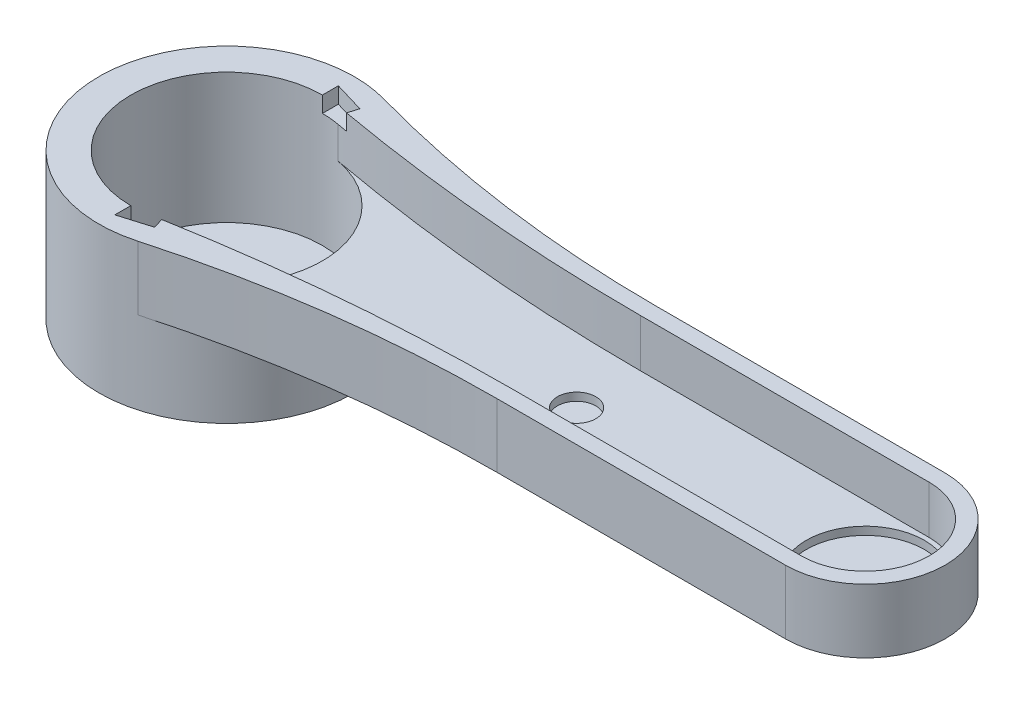
SolidWorks part; units mm, degrees
ref_plane "Front Plane" through (0, 0, 0) normal (0, 0, 1) x (1, 0, 0)
ref_plane "Top Plane" through (0, 0, 0) normal (0, 1, 0) x (1, 0, 0)
ref_plane "Right Plane" through (0, 0, 0) normal (1, 0, 0) x (0, 0, -1)
sketch "Sketch1" plane through (0, 0, 0) normal (0, 1, 0) x (1, 0, 0)
  line L0 (0, 0) -> (200, 0) construction
  line L1 (109.6, 25) -> (109.6, -25) construction
  line L2 (200, 25) -> (109.6, 25)
  line L3 (200, -25) -> (109.6, -25)
  line L4 (109.6, 20) -> (109.6, -20) construction
  line L5 (200, 20) -> (109.6, 20)
  line L6 (200, -20) -> (109.6, -20)
  circle A0 centre (0, 0) radius 30
  circle A1 centre (0, 0) radius 40
  circle A2 centre (109.6, 0) radius 25 construction
  circle A3 centre (200, 0) radius 25
  arc A4 (109.6, 25) -> (10.7476, 38.5291) centre (109.6, 392.9053) cw
  arc A5 (109.6, -25) -> (10.7476, -38.5291) centre (109.6, -392.9053) ccw
  circle A6 centre (109.6, 0) radius 20 construction
  circle A7 centre (200, 0) radius 20
  arc A8 (109.6, 20) -> (5.4293, 29.5046) centre (109.6, 595.608) cw
  arc A9 (109.6, -20) -> (5.4293, -29.5046) centre (109.6, -595.608) ccw
  dimension "D1" = 60
  dimension "D2" = 80
  dimension "D4" = 90.4
  dimension "D5" = 50
  dimension "D7" = 40
  dimension "D3" = 200
  dimension "D6" = 109.6
extrude "Boss-Extrude1" add sketch "Sketch1" along normal blind 15 contours A1 A9 A0 A8 | A8 L5 A3 L2 A4 A1 | L6 A9 A1 A5 L3 A3 | A7 L6 A3 L5
sketch "Sketch2" plane through (0, 0, 0) normal (0, -1, 0) x (1, 0, 0)
  circle A0 centre (0, 0) radius 40
  circle A1 centre (0, 0) radius 30
  arc A2 (10.7476, 38.5291) -> (10.7476, -38.5291) centre (0, 0) ccw construction
  arc A3 (5.4293, 29.5046) -> (5.4293, -29.5046) centre (0, 0) ccw construction
extrude "Boss-Extrude2" add sketch "Sketch2" along normal blind 25.8
sketch "Sketch3" plane through (0, -25.8, 0) normal (0, -1, 0) x (1, 0, 0)
  circle A0 centre (0, 0) radius 40 construction
  circle A1 centre (0, 0) radius 40
extrude "Boss-Extrude3" add sketch "Sketch3" along normal blind 5
sketch "Sketch4" plane through (0, 0, 0) normal (0, -1, 0) x (1, 0, 0)
  line L0 (200, 25) -> (109.6, 25) construction
  line L1 (200, -25) -> (109.6, -25) construction
  line L2 (200, 25) -> (109.6, 25)
  line L3 (200, -25) -> (109.6, -25)
  circle A0 centre (0, 0) radius 40 construction
  arc A1 (10.7476, 38.5291) -> (109.6, 25) centre (109.6, 392.9053) ccw construction
  circle A2 centre (200, 0) radius 25 construction
  arc A3 (109.6, -25) -> (10.7476, -38.5291) centre (109.6, -392.9053) ccw construction
  circle A4 centre (0, 0) radius 40
  arc A5 (10.7476, 38.5291) -> (109.6, 25) centre (109.6, 392.9053) ccw
  circle A6 centre (200, 0) radius 25
  arc A7 (109.6, -25) -> (10.7476, -38.5291) centre (109.6, -392.9053) ccw
  circle A8 centre (109.6, 0) radius 6
  circle A9 centre (200, 0) radius 18.5
  arc M1 (30.8954, -25.4061) -> (10.7476, -38.5291) centre (0, 0) cw
  arc M2 (10.7476, -38.5291) -> (109.6, -25) centre (109.6, -392.9053) cw
  line M3 (109.6, -25) -> (200, -25)
  arc M4 (200, -25) -> (200, 25) centre (200, 0) ccw
  line M5 (200, 25) -> (109.6, 25)
  arc M6 (109.6, 25) -> (10.7476, 38.5291) centre (109.6, 392.9053) cw
  arc M7 (10.7476, 38.5291) -> (30.8954, 25.4061) centre (0, 0) cw
  arc M8 (30.8954, 25.4061) -> (109.6, 20) centre (109.6, 595.608) ccw
  line M9 (109.6, 20) -> (200, 20)
  arc M10 (200, 20) -> (200, -20) centre (200, 0) cw
  line M11 (200, -20) -> (109.6, -20)
  arc M12 (109.6, -20) -> (30.8954, -25.4061) centre (109.6, -595.608) ccw
  dimension "D1" = 12
  dimension "D2" = 37
extrude "Boss-Extrude4" add sketch "Sketch4" along normal blind 5 contours A6 A4 A8 M9 M8 M12 M11 | A6 A9 M9 M11 M10 | A6 M4 M9 M10 M11 | A6 M5 M6 M7 M8 M9 | A6 M11 M12 M1 M2 M3
sketch "Sketch6" plane through (0, -5, 0) normal (0, -1, 0) x (1, 0, 0)
  circle A0 centre (109.6, 0) radius 6 construction
  circle A1 centre (109.6, 0) radius 6
  circle A2 centre (200, 0) radius 18.5 construction
  circle A3 centre (200, 0) radius 18.5
extrude "Boss-Extrude5" add sketch "Sketch6" against normal blind 2.5
sketch "Sketch7" plane through (0, 15, 0) normal (0, 1, 0) x (1, 0, 0)
  line L0 (0, -30) -> (0, -35)
  line L1 (0, -35) -> (9.5831, -32.1429)
  line L2 (0, -31.305) -> (8.5714, -28.7494) construction
  line L3 (9.5831, -32.1429) -> (8.5714, -28.7494)
  line L4 (0, 0) -> (-18.861, 0) construction
  line L5 (0, 31.305) -> (8.5714, 28.7494) construction
  line L6 (9.5831, 32.1429) -> (8.5714, 28.7494)
  line L7 (0, 35) -> (9.5831, 32.1429)
  line L8 (0, 30) -> (0, 35)
  circle A0 centre (0, 0) radius 30 construction
  circle A1 centre (0, 0) radius 30 construction
  arc A2 (0, -30) -> (8.5595, -28.753) centre (0, 0) ccw
  arc A3 (0, 30) -> (8.5595, 28.753) centre (0, 0) cw
  arc M14 (109.6, -20) -> (5.4293, -29.5046) centre (109.6, -595.608) ccw
  arc M15 (5.4293, -29.5046) -> (5.4293, 29.5046) centre (0, 0) cw
  arc M16 (5.4293, 29.5046) -> (109.6, 20) centre (109.6, 595.608) ccw
  dimension "D1" = 5
  dimension "D2" = 10
extrude "Cut-Extrude1" cut sketch "Sketch7" against normal blind 5 contours L1 L3 L0 M14 M15 | L8 L6 L7 M15 M16
sketch "Sketch8" plane through (0, -30.8, 0) normal (0, -1, 0) x (1, 0, 0)
  circle A0 centre (0, 0) radius 15 construction
  circle A1 centre (0, 15) radius 1.5
  circle A2 centre (15, 0) radius 1.5
  circle A3 centre (0, -15) radius 1.5
  circle A4 centre (-15, 0) radius 1.5
  point P14 (0, 0)
  dimension "D1" = 30
  dimension "D2" = 3
  dimension "D3" = 4
extrude "Cut-Extrude2" cut sketch "Sketch8" against normal through all both and the other way through all
sketch "Sketch9" plane through (0, -30.8, 0) normal (0, -1, 0) x (1, 0, 0)
  line L0 (-50, 0) -> (200, 0) construction
  circle A0 centre (200, 0) radius 18.5 construction
  circle A1 centre (-50, 0) radius 10
  circle A2 centre (200, 0) radius 10
  dimension "D2" = 20
  dimension "D1" = 250
